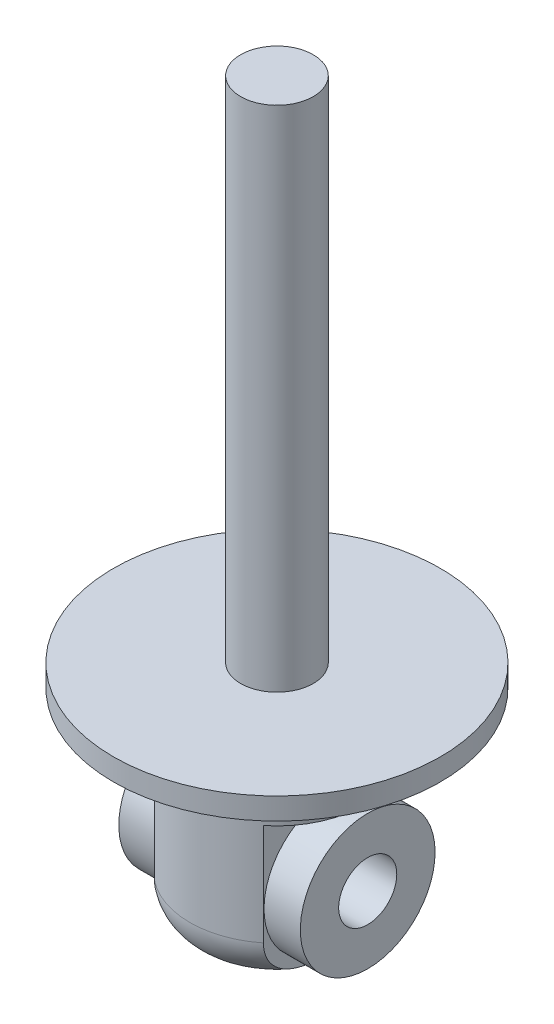
SolidWorks part; units mm, degrees
ref_plane "Front Plane" through (0, 0, 0) normal (0, 0, 1) x (1, 0, 0)
ref_plane "Top Plane" through (0, 0, 0) normal (0, 1, 0) x (1, 0, 0)
ref_plane "Right Plane" through (0, 0, 0) normal (1, 0, 0) x (0, 0, -1)
sketch "Sketch1" plane through (0, 0, 0) normal (0, 1, 0) x (1, 0, 0)
  circle A0 centre (0, 0) radius 22.5
extrude "Boss-Extrude3" add sketch "Sketch1" along normal blind 3
sketch "Sketch3" plane through (0, 3, 0) normal (0, 1, 0) x (1, 0, 0)
  circle A0 centre (0, 0) radius 5
extrude "Boss-Extrude4" add sketch "Sketch3" along normal blind 70
sketch "Sketch4" plane through (0, 0, 0) normal (0, -1, 0) x (1, 0, 0)
  circle A0 centre (0, 0) radius 12
extrude "Boss-Extrude5" add sketch "Sketch4" along normal blind 28
fillet "Fillet1" radius 6 1 edges at (0, -28, -12)
sketch "Sketch6" plane through (0, 0, 0) normal (0, 0, 1) x (1, 0, 0)
  line L0 (0, 0) -> (0, -28) construction
  line L1 (-6, -28) -> (6, -28) construction
  line L2 (27.5, -28) -> (27.5, -8)
  line L3 (27.5, -8) -> (7.5, -8)
  line L4 (7.5, -8) -> (7.5, -28)
  line L5 (7.5, -28) -> (27.5, -28)
  line L6 (-7.5, -8) -> (-7.5, -28)
  line L7 (-7.5, -28) -> (-27.5, -28)
  line L8 (-27.5, -28) -> (-27.5, -8)
  line L9 (-27.5, -8) -> (-7.5, -8)
  dimension "D1" = 15
  dimension "D2" = 20
  dimension "D3" = 20
  dimension "D4" = 20
extrude "Cut-Extrude1" cut sketch "Sketch6" against normal through all both and the other way through all
sketch "Sketch7" plane through (7.5, 0, 0) normal (1, 0, 0) x (0, 0, -1)
  line L0 (0, 0) -> (0, -28) construction
  line L1 (-6, -28) -> (6, -28) construction
  circle A0 centre (0, -18) radius 4
  dimension "D1" = 10
extrude "Cut-Extrude2" cut sketch "Sketch7" against normal blind 28
sketch "Sketch10" plane through (0, 0, 0) normal (1, 0, 0) x (0, 0, -1)
  circle A0 centre (0, -18) radius 9.2782
  circle A1 centre (0, -18) radius 4 construction
  circle A2 centre (0, -18) radius 4
extrude "Boss-Extrude6" add sketch "Sketch10" along normal mid plane 25
